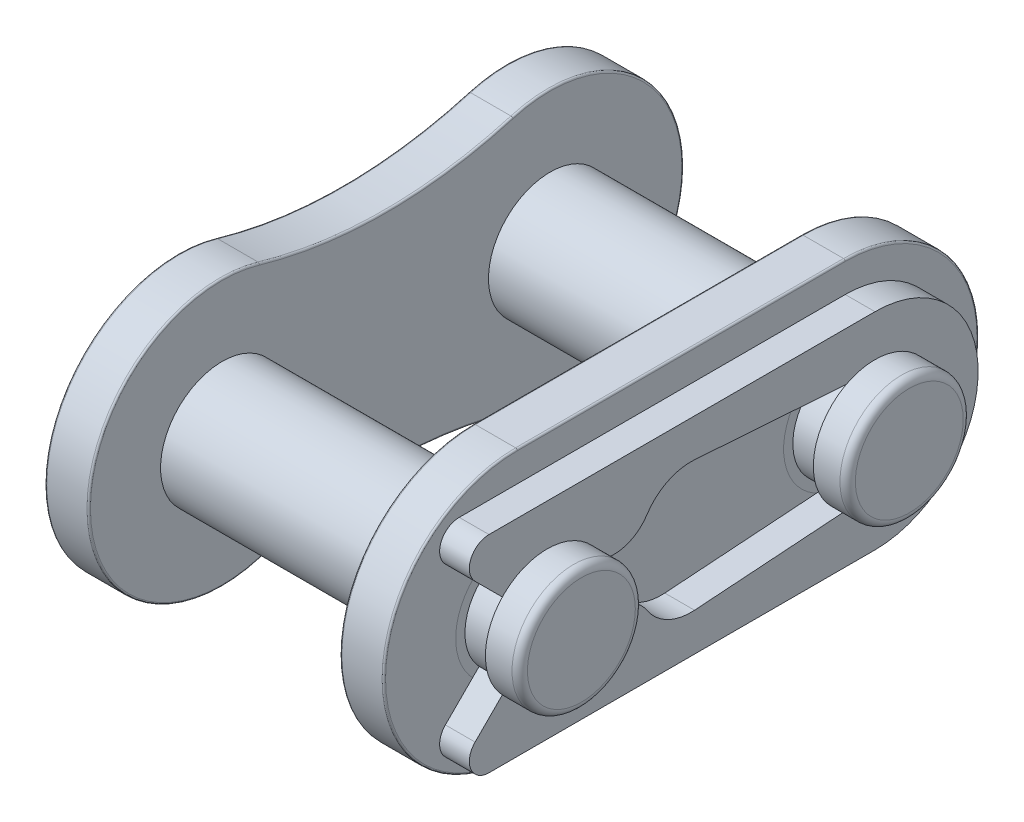
SolidWorks part; units mm, degrees
ref_plane "Front Plane" through (0, 0, 0) normal (0, 0, 1) x (1, 0, 0)
ref_plane "Top Plane" through (0, 0, 0) normal (0, 1, 0) x (1, 0, 0)
ref_plane "Right Plane" through (0, 0, 0) normal (1, 0, 0) x (0, 0, -1)
sketch "Sketch1" plane through (0, 0, 0) normal (1, 0, 0) x (0, 0, -1)
  line L0 (-4.7625, 0) -> (4.7625, 0) construction
  line L1 (-4.7625, 4.4069) -> (-4.7625, -4.4069) construction
  line L2 (4.7625, 4.4069) -> (4.7625, -4.4069) construction
  circle A0 centre (-4.7625, 0) radius 2.54 construction
  circle A1 centre (4.7625, 0) radius 2.54 construction
  circle A2 centre (-4.7625, 0) radius 1.7907 construction
  circle A3 centre (4.7625, 0) radius 1.7907 construction
  point P4 (0, 0)
  point P10 (-4.7625, 0)
  point P14 (4.7625, 0)
  dimension "For Roller Diameter" = 5.08
  dimension "Pin Diameter" = 3.5814
  dimension "For Plate Height" = 8.8138
  dimension "Pitch" = 9.525
sketch "Sketch2" plane through (0, 0, 0) normal (0, 1, 0) x (1, 0, 0)
  line L0 (-2.3812, 0) -> (2.3812, 0) construction
  line L1 (0, 4.7625) -> (6.7818, 4.7625) construction
  line L2 (0, 4.7625) -> (-5.9182, 4.7625) construction
  point P0 (-3.6513, 0)
  point P3 (0, 0)
  point P4 (3.6513, 0)
  dimension "For Roller Width" = 4.7625
  dimension "Plate Thickness" = 1.27
  dimension "Length L2" = 6.7818
  dimension "Length L1" = 5.9182
sketch "Sketch3" plane through (0, 0, 0) normal (1, 0, 0) x (0, 0, -1)
  line L0 (-4.7625, 3.8781) -> (-4.7625, -3.8781) construction
  line L1 (-4.7625, 3.8781) -> (4.7625, 3.8781)
  line L2 (-4.7625, -3.8781) -> (4.7625, -3.8781)
  arc A4 (-4.7625, 3.8781) -> (-4.7625, -3.8781) centre (-4.7625, 0) ccw
  arc A5 (4.7625, -3.8781) -> (4.7625, 3.8781) centre (4.7625, 0) ccw
  circle A8 centre (-4.7625, 0) radius 1.7907
  circle A9 centre (4.7625, 0) radius 1.7907
  circle A10 centre (-4.7625, 0) radius 1.7907 construction
  point P14 (0, 0)
  dimension "D1" = 7.7561
extrude "Boss-Extrude1" add sketch "Sketch3" along normal blind 1.27 from vertex at 3.6513 starting at point (3.6513, 0, 0)
fillet "Fillet1" radius 0.0508 8 edges at (4.9213, 0, -8.6406) (3.6513, 0, -8.6406) (4.9213, 0, 8.6406) (3.6513, 0, 8.6406) (4.9213, 3.8781, 0) (4.9213, -3.8781, 0) (3.6513, 3.8781, 0) (3.6513, -3.8781, 0)
sketch "Sketch4" plane through (0, 0, 0) normal (1, 0, 0) x (0, 0, -1)
  line L0 (0, 3.1956) -> (0, -3.1956) construction
  line L1 (0, 3.7459) -> (0, -3.7459) construction
  circle A0 centre (-4.7625, 0) radius 1.7907
  circle A1 centre (4.7625, 0) radius 1.7907
  circle A2 centre (-4.7625, 0) radius 1.7907 construction
  circle A3 centre (4.7625, 0) radius 1.7907 construction
  arc A4 (-3.6734, 3.722) -> (-3.6734, -3.722) centre (-4.7625, 0) ccw
  arc A5 (3.6734, -3.722) -> (3.6734, 3.722) centre (4.7625, 0) ccw
  arc A6 (-4.7625, 3.8781) -> (-4.7625, -3.8781) centre (-4.7625, 0) ccw construction
  arc A7 (4.7625, -3.8781) -> (4.7625, 3.8781) centre (4.7625, 0) ccw construction
  arc A8 (-3.6734, 3.722) -> (3.6734, 3.722) centre (0, 16.2752) ccw
  arc A9 (-3.6734, -3.722) -> (3.6734, -3.722) centre (0, -16.2752) cw
  circle A10 centre (-4.7625, 0) radius 4.4069 construction
  circle A11 centre (4.7625, 0) radius 4.4069 construction
  arc A12 (-3.5623, 4.2403) -> (3.5623, 4.2403) centre (0, 16.8255) ccw construction
  arc A13 (-3.5623, -4.2403) -> (3.5623, -4.2403) centre (0, -16.8255) cw construction
  point P26 (0, 0)
  dimension "D1" = 7.4917
extrude "Boss-Extrude2" add sketch "Sketch4" against normal blind 1.27 from vertex at -3.6513 separate body starting at point (-3.6513, 0, 0)
fillet "Fillet2" radius 0.0508 8 edges at (-4.9213, 3.1956, 0) (-4.9213, 0, -8.6406) (-4.9213, -3.1956, 0) (-3.6513, 3.1956, 0) (-3.6513, 0, -8.6406) (-3.6513, -3.1956, 0) (-4.9213, 0, 8.6406) (-3.6513, 0, 8.6406)
sketch "Sketch5" plane through (0, 0, 0) normal (1, 0, 0) x (0, 0, -1)
  circle A0 centre (-4.7625, 0) radius 1.7907
  circle A1 centre (4.7625, 0) radius 1.7907
  circle A2 centre (-4.7625, 0) radius 1.7907 construction
  circle A3 centre (4.7625, 0) radius 1.7907 construction
extrude "Boss-Extrude3" add sketch "Sketch5" along normal up to vertex (6.7818 mm away) and the other way up to vertex (5.9182 mm away) separate body up to point (6.7818, 0, -4.7625) other way up to point (-5.9182, 0, -4.7625)
fillet "Fillet3" radius 0.4477 1 edges at (-5.9182, 0, 2.9718)
fillet "Fillet4" radius 0.4477 1 edges at (-5.9182, 0, -6.5532)
sketch "Sketch6" plane through (0, 0, 0) normal (0, 1, 0) x (1, 0, 0)
  line L0 (-5.9182, -4.7625) -> (-4.9212, -4.7625) construction
  line L1 (-4.9212, -4.7625) -> (-3.6513, -4.7625) construction
  dimension "D2" = 0.9969
sketch "Sketch7" plane through (4.9213, 0, 0) normal (1, 0, 0) x (0, 0, -1)
  line L0 (4.7625, -2.9967) -> (-6.4493, -2.9967)
  line L1 (-6.8529, -2.0223) -> (-5.8723, -1.0417)
  line L2 (4.7625, 2.9967) -> (-6.4493, 2.9967)
  line L3 (-6.8529, 2.0223) -> (-5.8723, 1.0417)
  line L5 (-0.4791, 1.8923) -> (4.8687, 1.5184)
  line L6 (4.8687, -1.5184) -> (-0.4791, -1.8923)
  line L8 (4.7625, 0) -> (-4.7625, 0) construction
  line L9 (-5.8723, 1.0417) -> (-0.9254, 1.0417) construction
  arc A0 (4.7625, -2.9967) -> (4.7625, 2.9967) centre (4.7625, 0) ccw
  arc A1 (4.8687, -1.5184) -> (4.8687, 1.5184) centre (4.7625, 0) ccw
  arc A2 (-5.8723, -1.0417) -> (-3.6527, -1.0417) centre (-4.7625, 0) ccw
  arc A3 (-3.6527, 1.0417) -> (-5.8723, 1.0417) centre (-4.7625, 0) ccw
  arc A4 (-6.4493, 2.9967) -> (-6.8529, 2.0223) centre (-6.4493, 2.4259) ccw
  arc A5 (-6.4493, -2.9967) -> (-6.8529, -2.0223) centre (-6.4493, -2.4259) cw
  arc A8 (-6.987, 2.7351) -> (-6.987, -2.7351) centre (-4.7625, 0) ccw construction
  arc A9 (-3.6527, 1.0417) -> (-1.8624, 1.2019) centre (-2.8203, 1.8229) ccw
  arc A10 (-1.8624, 1.2019) -> (-0.4791, 1.8923) centre (-0.5852, 0.374) cw
  arc A11 (-3.6527, -1.0417) -> (-1.8624, -1.2019) centre (-2.8203, -1.8229) cw
  arc A12 (-1.8624, -1.2019) -> (-0.4791, -1.8923) centre (-0.5852, -0.374) ccw
  dimension "D3" = 5.9934
  dimension "D6" = 1.5221
  dimension "D7" = 1.5221
  dimension "D8" = 3.5255
  dimension "D9" = 0.5708
  dimension "D5" = 1.1416
  dimension "D1" = 4
  dimension "D2" = 4
  dimension "D10" = 45
extrude "Boss-Extrude4" add sketch "Sketch7" along normal offset from surface (0.8636 mm away) 0.9969 separate body up to face at (6.7818, 0, 2.9718)
sketch "Sketch8" plane through (4.9213, 0, 0) normal (1, 0, 0) x (0, 0, -1)
  circle A0 centre (-4.7625, 0) radius 1.7907
  circle A1 centre (-4.7625, 0) radius 1.5221
  circle A2 centre (-4.7625, 0) radius 1.7907 construction
  arc A3 (-3.6527, 1.0417) -> (-5.8723, 1.0417) centre (-4.7625, 0) ccw construction
extrude "Cut-Extrude1" cut sketch "Sketch8" along normal up to surface (0.8636 mm away) up to face at (5.7849, 0, 1.714)
sketch "Sketch9" plane through (4.9213, 0, 0) normal (1, 0, 0) x (0, 0, -1)
  circle A0 centre (4.7625, 0) radius 1.7907
  circle A1 centre (4.7625, 0) radius 1.5221
  circle A2 centre (-4.7625, 0) radius 1.7907 construction
  circle A3 centre (-4.7625, 0) radius 1.5221 construction
extrude "Cut-Extrude2" cut sketch "Sketch9" along normal up to surface (0.8636 mm away) up to face at (5.7849, 0, 1.714)
sketch "Sketch10" plane through (0, 0, 0) normal (0, 1, 0) x (1, 0, 0)
  line L0 (6.7818, -4.7625) -> (-5.9182, -4.7625) construction
  line L2 (-5.9182, -2.9718) -> (-5.9182, -6.5532) construction
  line L3 (6.7818, -2.9718) -> (6.7818, -6.5532) construction
  point P9 (-5.9182, -4.7625)
  point P10 (6.7818, -4.7625)
  dimension "D1" = 3.5814
fillet "Fillet5" radius 0.2238 1 edges at (6.7818, 0, 2.9718)
fillet "Fillet6" radius 0.2238 1 edges at (6.7818, 0, -6.5532)
ref_plane "Plane1" through (0, 0, 0) normal (1, 0, 0) x (0, 0, -1)
equation "\"D1@Sketch2\" = \"Plate Thickness@Sketch2\""
equation "\"D1@Fillet1\" = \"Plate Thickness@Sketch2\" * .04"
equation "\"D1@Boss-Extrude1\"=\"Plate Thickness@Sketch2\""
equation "\"D1@Sketch3\" = \"For Plate Height@Sketch1\" * .88"
equation "\"D1@Sketch4\" = \"For Plate Height@Sketch1\" * .85"
equation "\"D1@Boss-Extrude2\"=\"Plate Thickness@Sketch2\""
equation "\"D1@Fillet2\"=\"D1@Fillet1\""
equation "\"D1@Fillet3\"=\"Pin Diameter@Sketch1\"*.125"
equation "\"D1@Fillet4\"=\"D1@Fillet3\""
equation "\"D1@Sketch6\" = \"Plate Thickness@Sketch2\""
equation "\"D1@Boss-Extrude4\"=\"D2@Sketch6\""
equation "\"D6@Sketch7\"=(\"Pin Diameter@Sketch1\"/2)*.85"
equation "\"D7@Sketch7\"=\"D6@Sketch7\""
equation "\"D3@Sketch7\"=\"For Plate Height@Sketch1\"*.68"
equation "\"D8@Sketch7\"=(\"For Plate Height@Sketch1\"/2)*.8"
equation "\"D9@Sketch7\"=\"D5@Sketch7\"/2"
equation "\"D1@Fillet6\"=\"D1@Fillet5\""
equation "\"D1@Fillet5\"=\"D1@Fillet3\"*.5"
equation "\"D5@Sketch7\"=\"D7@Sketch7\"*.75"
equation "\"D1@Sketch10\"=\"Pin Diameter@Sketch1\""
